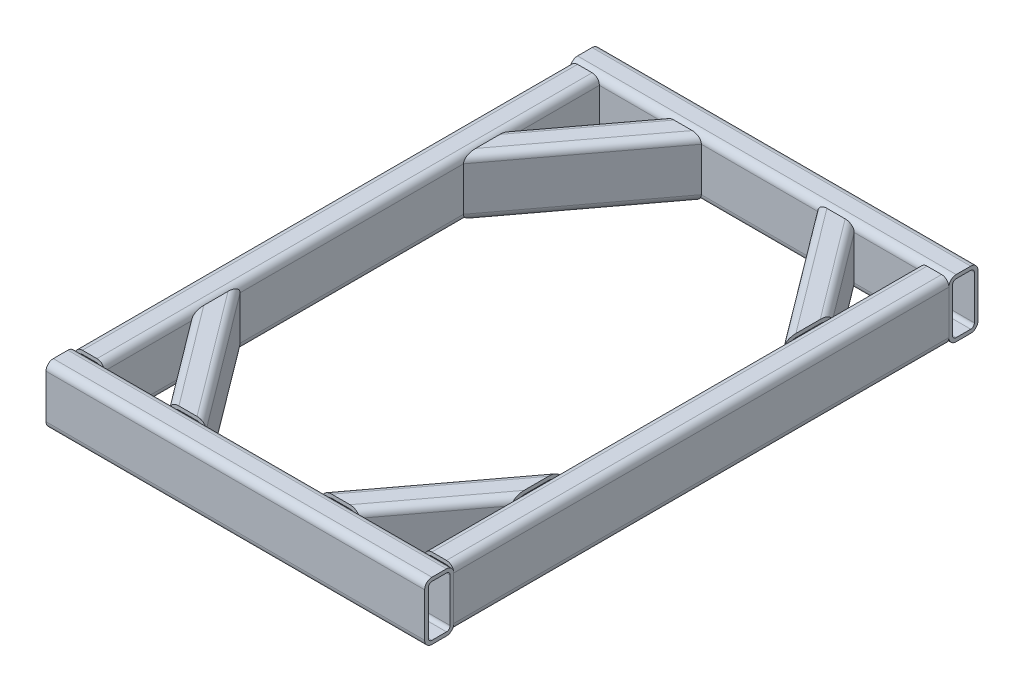
SolidWorks part; units mm, degrees
ref_plane "Front Plane" through (0, 0, 0) normal (0, 0, 1) x (1, 0, 0)
ref_plane "Top Plane" through (0, 0, 0) normal (0, 1, 0) x (1, 0, 0)
ref_plane "Right Plane" through (0, 0, 0) normal (1, 0, 0) x (0, 0, -1)
sketch "Sketch1" plane through (0, 0, 0) normal (0, 1, 0) x (1, 0, 0)
  line L0 (-304.8, 203.2) -> (-114.3, 457.2)
  line L1 (-304.8, -457.2) -> (304.8, -457.2)
  line L2 (-304.8, -457.2) -> (-304.8, 457.2)
  line L3 (-304.8, 457.2) -> (304.8, 457.2)
  line L4 (304.8, -457.2) -> (304.8, 457.2)
  line L5 (-304.8, -457.2) -> (304.8, 457.2) construction
  line L6 (-304.8, 457.2) -> (304.8, -457.2) construction
  line L7 (0, 457.2) -> (0, -457.2) construction
  line L8 (-304.8, -203.2) -> (-114.3, -457.2)
  line L9 (304.8, -203.2) -> (114.3, -457.2)
  line L10 (304.8, 203.2) -> (114.3, 457.2)
  point P0 (0, 0)
  dimension "D1" = 914.4
  dimension "D2" = 609.6
  dimension "D3" = 190.5
  dimension "D4" = 254
  dimension "D5" = 254
  dimension "D6" = 190.5
other "Structural Member1"
ref_plane "Plane1" through (-304.8, 0, -457.2) normal (1, 0, 0) x (0, 0, -1)
sketch "Sketch16" plane through (-304.8, 0, -457.2) normal (1, 0, 0) x (0, 0, -1)
  line L0 (-12.7, -44.45) -> (12.7, -44.45)
  line L1 (-19.05, -38.1) -> (-19.05, 38.1)
  line L2 (12.7, 44.45) -> (-12.7, 44.45)
  line L3 (19.05, 38.1) -> (19.05, -38.1)
  line L4 (-12.7, -50.8) -> (12.7, -50.8)
  line L5 (-25.4, -38.1) -> (-25.4, 38.1)
  line L6 (12.7, 50.8) -> (-12.7, 50.8)
  line L7 (25.4, 38.1) -> (25.4, -38.1)
  line L8 (0, 0) -> (25.4, 0) construction
  line L9 (0, 0) -> (0, 50.8) construction
  arc A0 (25.4, 38.1) -> (12.7, 50.8) centre (12.7, 38.1) ccw
  arc A1 (12.7, -50.8) -> (25.4, -38.1) centre (12.7, -38.1) ccw
  arc A2 (-25.4, -38.1) -> (-12.7, -50.8) centre (-12.7, -38.1) ccw
  arc A3 (-12.7, 50.8) -> (-25.4, 38.1) centre (-12.7, 38.1) ccw
  arc A4 (-12.7, 44.45) -> (-19.05, 38.1) centre (-12.7, 38.1) ccw
  arc A5 (19.05, 38.1) -> (12.7, 44.45) centre (12.7, 38.1) ccw
  arc A6 (12.7, -44.45) -> (19.05, -38.1) centre (12.7, -38.1) ccw
  arc A7 (-19.05, -38.1) -> (-12.7, -44.45) centre (-12.7, -38.1) ccw
  point P3 (0, -50.8)
  point P4 (-25.4, 0)
  point P5 (0, 0)
  point P6 (25.4, -50.8)
  point P7 (-25.4, -50.8)
  point P8 (-25.4, 50.8)
  point P33 (0, 0)
  point P35 (25.4, 50.8)
  point P36 (25.4, 0)
  point P37 (0, 50.8)
  dimension "D1" = 12.7
  dimension "Thickness" = 6.35
  dimension "V_leg" = 101.6
  dimension "H_leg" = 50.8
sketch3d "3DSketch1" plane through (0, 0, 0) normal (0, 0, 1) x (1, 0, 0)
  dimension "D1" = 330.2
